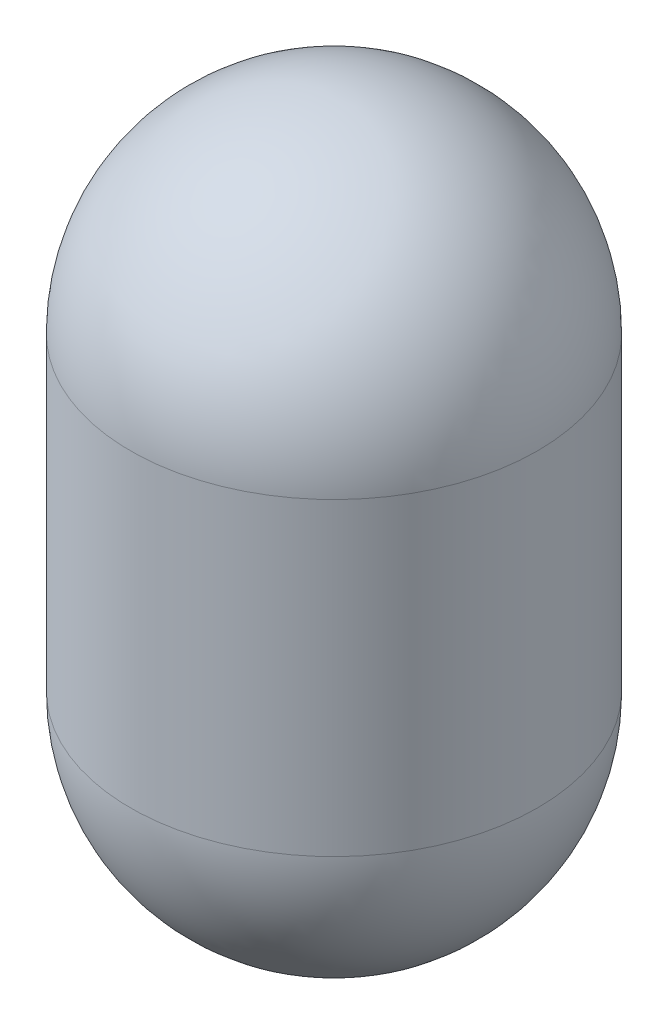
SolidWorks part; units mm, degrees
ref_plane "Front Plane" through (0, 0, 0) normal (0, 0, 1) x (1, 0, 0)
ref_plane "Top Plane" through (0, 0, 0) normal (0, 1, 0) x (1, 0, 0)
ref_plane "Right Plane" through (0, 0, 0) normal (1, 0, 0) x (0, 0, -1)
sketch "Sketch1" plane through (0, 0, 0) normal (0, 0, 1) x (1, 0, 0)
  line L0 (125, 315) -> (125, -125) construction
  line L2 (0, 0) -> (0, 190)
  line L5 (10, 0) -> (10, 190)
  line L6 (125, -115) -> (125, -125)
  line L7 (125, 305) -> (125, 315)
  arc A0 (125, 315) -> (0, 190) centre (125, 190) ccw
  arc A1 (0, 0) -> (125, -125) centre (125, 0) ccw
  arc A2 (10, 0) -> (125, -115) centre (125, 0) ccw
  arc A3 (125, 305) -> (10, 190) centre (125, 190) ccw
  dimension "D1" = 440
  dimension "D2" = 125
  dimension "D3" = 10
revolve "Revolve1" add sketch "Sketch1" angle 360 about L0
